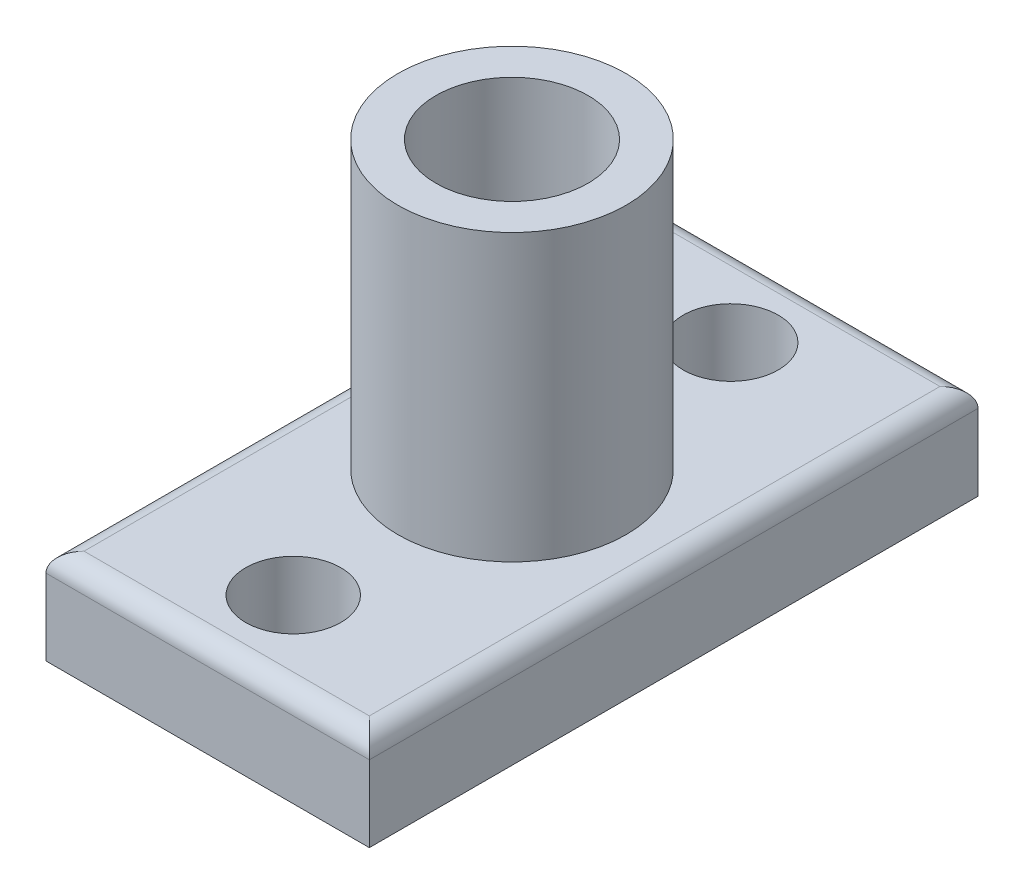
SolidWorks part; units mm, degrees
ref_plane "Front Plane" through (0, 0, 0) normal (0, 0, 1) x (1, 0, 0)
ref_plane "Top Plane" through (0, 0, 0) normal (0, 1, 0) x (1, 0, 0)
ref_plane "Right Plane" through (0, 0, 0) normal (1, 0, 0) x (0, 0, -1)
sketch "Sketch1" plane through (0, 0, 0) normal (0, 1, 0) x (1, 0, 0)
  line L1 (-8.5, -16) -> (8.5, -16)
  line L2 (-8.5, -16) -> (-8.5, 16)
  line L3 (-8.5, 16) -> (8.5, 16)
  line L4 (8.5, -16) -> (8.5, 16)
  line L5 (-8.5, -16) -> (8.5, 16) construction
  line L6 (-8.5, 16) -> (8.5, -16) construction
  circle A0 centre (0, 0) radius 6 construction
  circle A1 centre (0, 11.5) radius 2.5
  circle A2 centre (0, -11.5) radius 2.5
  point P0 (0, 0)
  dimension "D3" = 12
  dimension "D4" = 5
  dimension "D6" = 4.5
  dimension "D1" = 32
  dimension "D2" = 17
  dimension "D5" = 4.5
extrude "Boss-Extrude1" add sketch "Sketch1" along normal blind 5
sketch "Sketch2" plane through (0, 5, 0) normal (0, 1, 0) x (1, 0, 0)
  circle A0 centre (0, 0) radius 6
  circle A1 centre (0, 0) radius 4
  dimension "D1" = 8
  dimension "D2" = 12
extrude "Boss-Extrude2" add sketch "Sketch2" along normal blind 15
fillet "Fillet1" radius 1 4 edges at (0, 5, -16) (0, 5, 16) (-8.5, 5, 0) (8.5, 5, 0)
